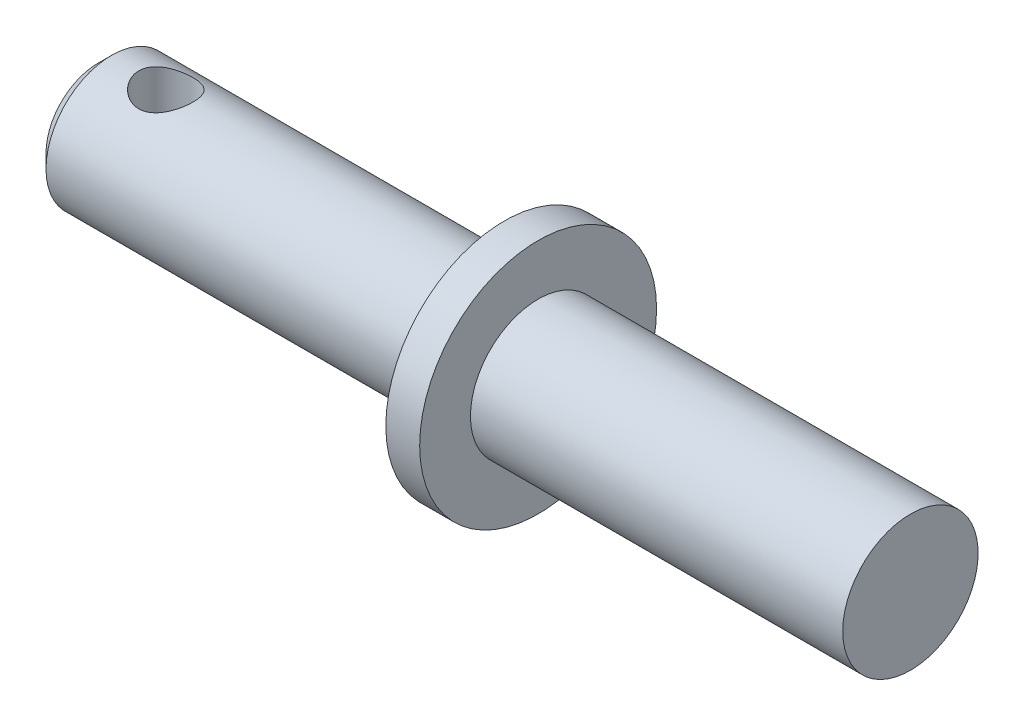
SolidWorks part; units mm, degrees
material "25CrMo4"
ref_plane "Plan de face" through (0, 0, 0) normal (0, 0, 1) x (1, 0, 0)
ref_plane "Plan de dessus" through (0, 0, 0) normal (0, 1, 0) x (1, 0, 0)
ref_plane "Plan de droite" through (0, 0, 0) normal (1, 0, 0) x (0, 0, -1)
sketch "Esquisse1" plane through (0, 0, 0) normal (0, 0, 1) x (1, 0, 0)
  line L0 (0, 0) -> (56.3636, 0) construction
  line L1 (55, 0) -> (55, 10)
  line L2 (55, 10) -> (0, 10)
  line L3 (0, 10) -> (0, 17.5)
  line L4 (0, 17.5) -> (-5, 17.5)
  line L5 (-5, 17.5) -> (-5, 9.7)
  line L6 (-5, 9.7) -> (-63, 9.7)
  line L7 (-63, 9.7) -> (-65, 7.7)
  line L8 (-65, 7.7) -> (-65, 0)
  line L9 (-65, 0) -> (55, 0)
  dimension "D1" = 20
  dimension "D2" = 19.4
  dimension "D3" = 45
  dimension "D4" = 2
  dimension "D5" = 35
  dimension "D6" = 5
  dimension "D7" = 55
  dimension "D8" = 120
revolve "Révolution1" add sketch "Esquisse1" angle 360 about L0
fillet "Congé1" radius 2 1 edges at (-5, 0, 9.7)
sketch "Esquisse2" plane through (0, 0, 0) normal (0, 1, 0) x (1, 0, 0)
  line L1 (-65, 7.7) -> (-65, -7.7) construction
  circle A0 centre (-55, 0) radius 4
  dimension "D1" = 8
  dimension "D2" = 10
extrude "Enlèv. mat.-Extru.1" cut sketch "Esquisse2" against normal through all both and the other way through all
